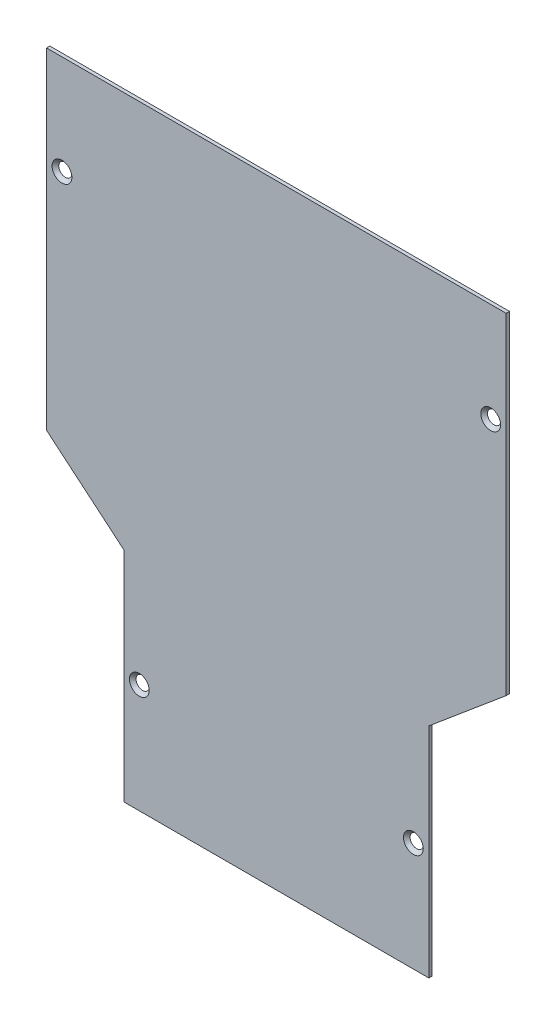
SolidWorks part; units mm, degrees
ref_plane "Plano frontal" through (0, 0, 0) normal (0, 0, 1) x (1, 0, 0)
ref_plane "Plano superior" through (0, 0, 0) normal (0, 1, 0) x (1, 0, 0)
ref_plane "Plano direito" through (0, 0, 0) normal (1, 0, 0) x (0, 0, -1)
sketch "Esboço1" plane through (0, 0, 0) normal (0, 0, 1) x (1, 0, 0)
  line L5 (100.8609, 140.9966) -> (-107.1391, 140.9966)
  line L6 (-107.1391, 140.9966) -> (-107.1391, -8.8424)
  line L7 (-107.1391, -8.8424) -> (-72.1391, -38.2109)
  line L8 (-72.1391, -38.2109) -> (-72.1391, -137.0034)
  line L9 (-72.1391, -137.0034) -> (65.8609, -137.0034)
  line L10 (65.8609, -38.2109) -> (65.8609, -137.0034)
  line L11 (100.8609, -8.8424) -> (65.8609, -38.2109)
  line L12 (100.8609, 140.9966) -> (100.8609, -8.8424)
extrude "Ressalto-extrusão1" add sketch "Esboço1" along normal blind 1.5
sketch "Esboço2" plane through (0, 0, 1.5) normal (0, 0, 1) x (1, 0, 0)
  line L0 (-3.1391, -209.543) -> (-3.1391, 236.4713) construction
  line L2 (100.8609, 140.9966) -> (-107.1391, 140.9966) construction
  line L3 (-107.1391, 140.9966) -> (-107.1391, -8.8424) construction
  line L4 (-72.1391, -38.2109) -> (-72.1391, -137.0034) construction
  circle A0 centre (-65.1391, -87.6072) radius 3
  circle A1 centre (-100.1391, 95.9966) radius 3
  circle A2 centre (93.8609, 95.9966) radius 3
  circle A3 centre (58.8609, -87.6072) radius 3
  dimension "D1" = 45
  dimension "D2" = 7
  dimension "D3" = 7
hole_wizard "Escareado para parafuso Allen sextavado escareado de M41" positions "3DSketch1" profile "Esboço3" countersink size "M4" standard "ISO" end condition through all
sketch3d "3DSketch1"
  point P0 (-100.1391, 95.9966, 1.5)
  point P3 (93.8609, 95.9966, 1.5)
  point P6 (58.8609, -87.6072, 1.5)
  point P9 (-65.1391, -87.6072, 1.5)
sketch "Esboço3" plane through (-100.1391, 95.9966, 1.5) normal (1, 0, 0) x (0, -1, 0)
  line L0 (0, 0) -> (0, 1.5)
  line L1 (0, 1.5) -> (2.25, 1.5)
  line L2 (2.25, 1.5) -> (2.25, 2.23)
  line L3 (2.25, 2.23) -> (4.48, 0)
  line L5 (4.48, 0) -> (0, 0)
  line L6 (-2.25, 2.23) -> (-4.48, 0) construction
  line L11 (0, -6.35) -> (0, 107.95) construction
  dimension "Thru Hole Dia." = 4.5
  dimension "Thru Hole Depth" = 1.5
  dimension "Near C'Sink Dia." = 8.96
  dimension "Near C'Sink Angle" = 90
